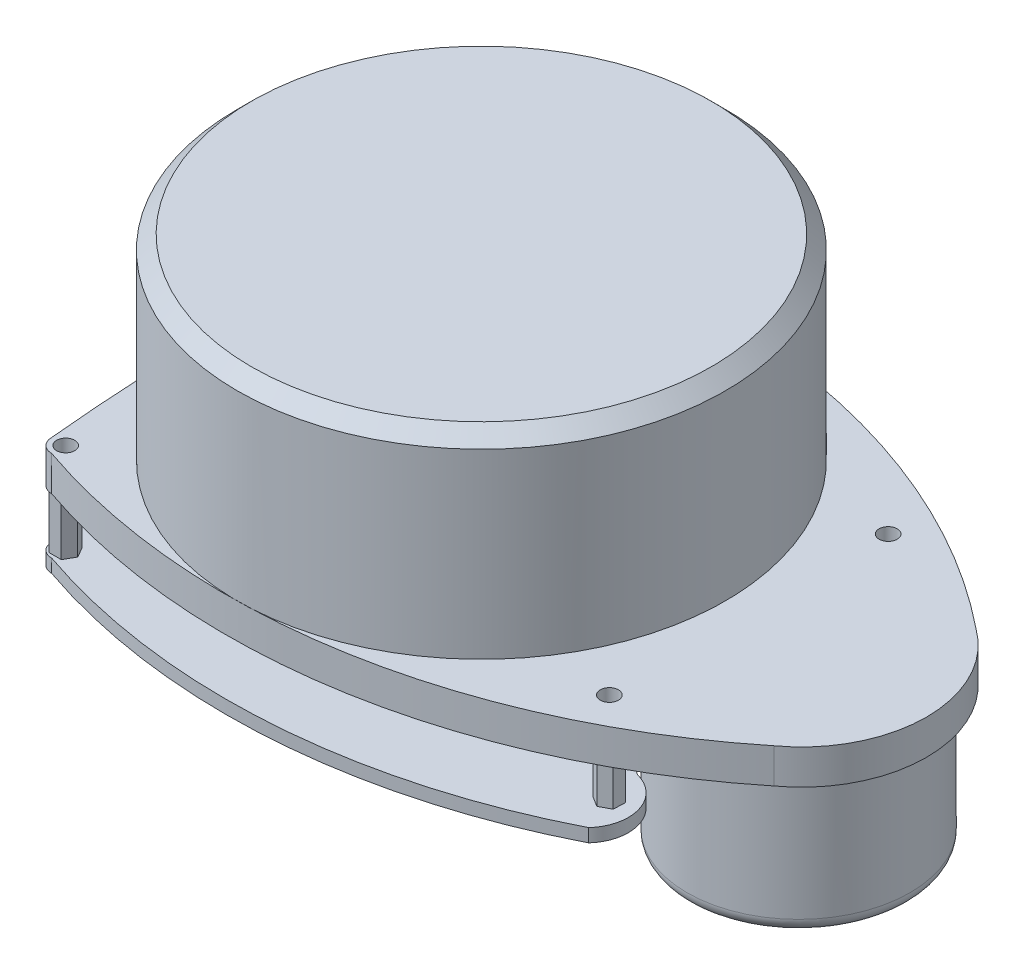
SolidWorks part; units mm, degrees
ref_plane "Front Plane" through (0, 0, 0) normal (0, 0, 1) x (1, 0, 0)
ref_plane "Top Plane" through (0, 0, 0) normal (0, 1, 0) x (1, 0, 0)
ref_plane "Right Plane" through (0, 0, 0) normal (1, 0, 0) x (0, 0, -1)
sketch "Sketch3" plane through (0, 0, 0) normal (0, 1, 0) x (1, 0, 0)
  line L0 (49.25, 0) -> (-49.25, 0) construction
  line L1 (49.25, 30) -> (-49.25, 30) construction
  line L2 (49.25, 30) -> (49.25, -30) construction
  line L3 (49.25, -30) -> (-49.25, -30) construction
  line L4 (-49.25, 30) -> (-49.25, -30) construction
  line L5 (49.25, 30) -> (-49.25, -30) construction
  line L6 (49.25, -30) -> (-49.25, 30) construction
  circle A0 centre (-46.25, 28) radius 1.3
  circle A1 centre (-46.25, -28) radius 1.3
  circle A2 centre (23.75, 20) radius 1.3
  circle A3 centre (23.75, -20) radius 1.3
  arc A5 (-46.25, 30) -> (-48.25, 28) centre (-46.25, 28) ccw
  arc A6 (-48.25, -28) -> (-46.25, -30) centre (-46.25, -28) ccw
  arc A7 (41.8569, 14.5021) -> (-46.25, 30) centre (-16.1861, -57.2803) ccw
  arc A8 (41.8569, -14.5021) -> (-46.25, -30) centre (-16.1861, 57.2803) cw
  arc A9 (-48.25, 28) -> (-48.25, -28) centre (239.7946, 0) ccw
  circle A10 centre (-14.25, 0) radius 35 construction
  arc A11 (41.8569, -14.5021) -> (41.8569, 14.5021) centre (31.3301, 0) ccw
  point P0 (0, 0)
  dimension "D3" = 2.6
  dimension "D12" = 70
  dimension "D1" = 98.5
  dimension "D2" = 60
  dimension "D4" = 56
  dimension "D5" = 28
  dimension "D6" = 70
  dimension "D7" = 70
  dimension "D8" = 40
  dimension "D9" = 20
  dimension "D10" = 3
extrude "Boss-Extrude2" add sketch "Sketch3" along normal blind 5
sketch "Sketch5" plane through (0, 5, 0) normal (0, 1, 0) x (1, 0, 0)
  line L0 (-49.6077, 0) -> (49.25, 0) construction
  arc A0 (-48.25, 28) -> (-48.25, -28) centre (239.7946, 0) ccw construction
  arc A1 (41.8569, -14.5021) -> (41.8569, 14.5021) centre (31.3301, 0) ccw construction
  circle A2 centre (-14.6077, 0) radius 35
  dimension "D1" = 70
extrude "Boss-Extrude4" add sketch "Sketch5" along normal blind 28.1
chamfer "Chamfer2" distance 2 angle 45 1 edges at (-14.6077, 33.1, 35)
sketch "Sketch6" plane through (0, 0, 0) normal (0, -1, 0) x (1, 0, 0)
  line L0 (-49.6077, 0) -> (4.5785, 0) construction
  arc A0 (-48.25, 28) -> (-48.25, -28) centre (239.7946, 0) ccw construction
  circle A1 centre (-14.6077, 0) radius 25
  dimension "D2" = 50
  dimension "D1" = 35
extrude "Boss-Extrude5" add sketch "Sketch6" along normal blind 3
chamfer "Chamfer3" distance 1 angle 45 1 edges at (-14.6077, -3, -25)
sketch "Sketch7" plane through (0, 0, 0) normal (0, -1, 0) x (1, 0, 0)
  line L0 (49.25, 0) -> (-13.8287, 0) construction
  circle A0 centre (30.8923, 0) radius 16
  arc A1 (41.8569, -14.5021) -> (41.8569, 14.5021) centre (31.3301, 0) ccw construction
  dimension "D1" = 32
  dimension "D2" = 80.5
extrude "Boss-Extrude6" add sketch "Sketch7" along normal blind 20
sketch "Sketch8" plane through (0, -20, 0) normal (0, -1, 0) x (1, 0, 0)
  circle A0 centre (30.8923, 0) radius 3.55
  circle A1 centre (30.8923, 0) radius 16 construction
  dimension "D1" = 7.1
extrude "Boss-Extrude7" add sketch "Sketch8" along normal blind 2
fillet "Fillet1" radius 2 1 edges at (30.8923, -20, -16)
sketch "Sketch9" plane through (0, 0, 0) normal (0, -1, 0) x (1, 0, 0)
  line L1 (22.6677, -18.6477) -> (22.0377, -20.2611)
  line L2 (22.0377, -20.2611) -> (23.12, -21.6134)
  line L3 (23.12, -21.6134) -> (24.8323, -21.3523)
  line L4 (24.8323, -21.3523) -> (25.4623, -19.7389)
  line L5 (25.4623, -19.7389) -> (24.38, -18.3866)
  line L6 (24.38, -18.3866) -> (22.6677, -18.6477)
  line L7 (-47.2786, -26.6064) -> (-47.9712, -28.194)
  line L8 (-47.9712, -28.194) -> (-46.9426, -29.5876)
  line L9 (-46.9426, -29.5876) -> (-45.2214, -29.3936)
  line L10 (-45.2214, -29.3936) -> (-44.5288, -27.806)
  line L11 (-44.5288, -27.806) -> (-45.5574, -26.4124)
  line L12 (-45.5574, -26.4124) -> (-47.2786, -26.6064)
  line L13 (-47.1173, 29.4993) -> (-47.9821, 27.9985)
  line L14 (-47.9821, 27.9985) -> (-47.1147, 26.4993)
  line L15 (-47.1147, 26.4993) -> (-45.3827, 26.5007)
  line L16 (-45.3827, 26.5007) -> (-44.5179, 28.0015)
  line L17 (-44.5179, 28.0015) -> (-45.3853, 29.5007)
  line L18 (-45.3853, 29.5007) -> (-47.1173, 29.4993)
  line L19 (22.22, 20.8119) -> (22.2819, 19.081)
  line L20 (22.2819, 19.081) -> (23.8118, 18.2691)
  line L21 (23.8118, 18.2691) -> (25.28, 19.1881)
  line L22 (25.28, 19.1881) -> (25.2181, 20.919)
  line L23 (25.2181, 20.919) -> (23.6882, 21.7309)
  line L24 (23.6882, 21.7309) -> (22.22, 20.8119)
  circle A0 centre (-46.25, -28) radius 1.3 construction
  circle A1 centre (23.75, -20) radius 1.3 construction
  circle A2 centre (23.75, 20) radius 1.3 construction
  circle A3 centre (-46.25, 28) radius 1.3 construction
  circle A4 centre (-46.25, -28) radius 1.3
  circle A5 centre (23.75, -20) radius 1.3
  circle A6 centre (23.75, 20) radius 1.3
  circle A7 centre (-46.25, 28) radius 1.3
  circle A8 centre (23.75, -20) radius 1.5 construction
  circle A9 centre (-46.25, -28) radius 1.5 construction
  circle A10 centre (-46.25, 28) radius 1.5 construction
  circle A11 centre (23.75, 20) radius 1.5 construction
  dimension "D2" = 3
  dimension "D3" = 3
  dimension "D1" = 3
extrude "Boss-Extrude8" add sketch "Sketch9" along normal blind 8
ref_plane "Plane2" through (0, -8, 0) normal (0, -1, 0) x (-1, 0, 0)
sketch "Sketch11" plane through (0, -8, 0) normal (0, -1, 0) x (-1, 0, 0)
  arc A0 (46.25, 30) -> (-41.8569, 14.5021) centre (16.1861, -57.2803) ccw construction
  arc A1 (-41.8569, -14.5021) -> (46.25, -30) centre (16.1861, 57.2803) ccw construction
  arc A2 (48.25, -28) -> (48.25, 28) centre (-239.7946, 0) ccw construction
  arc A3 (46.25, -30) -> (48.25, -28) centre (46.25, -28) ccw construction
  arc A4 (48.25, 28) -> (46.25, 30) centre (46.25, 28) ccw construction
  arc A5 (46.25, 30) -> (-25.7467, 24.9592) centre (16.1861, -57.2803) ccw
  arc A6 (-25.7467, -24.9592) -> (46.25, -30) centre (16.1861, 57.2803) ccw
  arc A7 (48.25, -28) -> (48.25, 28) centre (-239.7946, 0) ccw
  arc A8 (46.25, -30) -> (48.25, -28) centre (46.25, -28) ccw
  arc A9 (48.25, 28) -> (46.25, 30) centre (46.25, 28) ccw
  circle A10 centre (-30.8923, 0) radius 16 construction
  circle A11 centre (-30.8923, 0) radius 16 construction
  arc A12 (-22.6982, -14.8948) -> (-24.4748, 15.7422) centre (-30.8923, 0) ccw
  arc A13 (-25.7467, 24.9592) -> (-24.4748, 15.7422) centre (-22.6982, 20.6836) ccw
  arc A14 (-22.6982, -14.8948) -> (-25.7467, -24.9592) centre (-21.1913, -20.8452) ccw
  circle A15 centre (-23.75, 20) radius 1.3 construction
  circle A16 centre (-30.8923, 0) radius 17 construction
  circle A17 centre (-23.75, -20) radius 1.3 construction
  circle A18 centre (46.25, -28) radius 1.3 construction
  circle A19 centre (46.25, 28) radius 1.3 construction
  circle A20 centre (-23.75, 20) radius 1.3
  circle A21 centre (-23.75, -20) radius 1.3
  circle A22 centre (46.25, -28) radius 1.3
  circle A23 centre (46.25, 28) radius 1.3
  point P23 (-13.8923, 0)
  dimension "D1" = 1
extrude "Boss-Extrude9" add sketch "Sketch11" along normal blind 1.9
sketch "Sketch12" plane through (0, -9.9, 0) normal (0, -1, 0) x (1, 0, 0)
  line L0 (25.28, 19.1881) -> (25.2181, 20.919) construction
  line L1 (23.8118, 18.2691) -> (25.28, 19.1881) construction
  line L2 (25.2181, 20.919) -> (23.6882, 21.7309) construction
  line L3 (23.6882, 21.7309) -> (22.22, 20.8119) construction
  line L4 (22.22, 20.8119) -> (22.2819, 19.081) construction
  line L5 (22.2819, 19.081) -> (23.8118, 18.2691) construction
  line L6 (-47.1173, 29.4993) -> (-47.9821, 27.9985) construction
  line L7 (-45.3853, 29.5007) -> (-47.1173, 29.4993) construction
  line L8 (-47.9821, 27.9985) -> (-47.1147, 26.4993) construction
  line L9 (-44.5179, 28.0015) -> (-45.3853, 29.5007) construction
  line L10 (-45.3827, 26.5007) -> (-44.5179, 28.0015) construction
  line L11 (-47.1147, 26.4993) -> (-45.3827, 26.5007) construction
  line L12 (-47.9712, -28.194) -> (-46.9426, -29.5876) construction
  line L13 (-46.9426, -29.5876) -> (-45.2214, -29.3936) construction
  line L14 (-45.2214, -29.3936) -> (-44.5288, -27.806) construction
  line L15 (-44.5288, -27.806) -> (-45.5574, -26.4124) construction
  line L16 (-45.5574, -26.4124) -> (-47.2786, -26.6064) construction
  line L17 (-47.2786, -26.6064) -> (-47.9712, -28.194) construction
  line L18 (23.12, -21.6134) -> (24.8323, -21.3523) construction
  line L19 (24.8323, -21.3523) -> (25.4623, -19.7389) construction
  line L20 (25.4623, -19.7389) -> (24.38, -18.3866) construction
  line L21 (22.0377, -20.2611) -> (23.12, -21.6134) construction
  line L22 (22.6677, -18.6477) -> (22.0377, -20.2611) construction
  line L23 (25.28, 19.1881) -> (25.2181, 20.919)
  line L24 (23.8118, 18.2691) -> (25.28, 19.1881)
  line L25 (25.2181, 20.919) -> (23.6882, 21.7309)
  line L26 (23.6882, 21.7309) -> (22.22, 20.8119)
  line L27 (22.22, 20.8119) -> (22.2819, 19.081)
  line L28 (22.2819, 19.081) -> (23.8118, 18.2691)
  line L29 (-47.1173, 29.4993) -> (-47.9821, 27.9985)
  line L30 (-45.3853, 29.5007) -> (-47.1173, 29.4993)
  line L31 (-47.9821, 27.9985) -> (-47.1147, 26.4993)
  line L32 (-44.5179, 28.0015) -> (-45.3853, 29.5007)
  line L33 (-45.3827, 26.5007) -> (-44.5179, 28.0015)
  line L34 (-47.1147, 26.4993) -> (-45.3827, 26.5007)
  line L35 (-47.9712, -28.194) -> (-46.9426, -29.5876)
  line L36 (-46.9426, -29.5876) -> (-45.2214, -29.3936)
  line L37 (-45.2214, -29.3936) -> (-44.5288, -27.806)
  line L38 (-44.5288, -27.806) -> (-45.5574, -26.4124)
  line L39 (-45.5574, -26.4124) -> (-47.2786, -26.6064)
  line L40 (-47.2786, -26.6064) -> (-47.9712, -28.194)
  line L41 (23.12, -21.6134) -> (24.8323, -21.3523)
  line L42 (24.8323, -21.3523) -> (25.4623, -19.7389)
  line L43 (25.4623, -19.7389) -> (24.38, -18.3866)
  line L44 (22.0377, -20.2611) -> (23.12, -21.6134)
  line L45 (22.6677, -18.6477) -> (22.0377, -20.2611)
  line L46 (24.38, -18.3866) -> (22.6677, -18.6477) construction
  line L47 (24.38, -18.3866) -> (22.6677, -18.6477)
  arc A8 (-48.25, -28) -> (-46.25, -30) centre (-46.25, -28) ccw
  arc A9 (-46.25, -30) -> (25.7467, -24.9592) centre (-16.1861, 57.2803) ccw
  arc A10 (25.7467, -24.9592) -> (24.4748, -15.7422) centre (22.6982, -20.6836) ccw
  arc A11 (22.6982, 14.8948) -> (24.4748, -15.7422) centre (30.8923, 0) ccw
  arc A12 (22.6982, 14.8948) -> (25.7467, 24.9592) centre (21.1913, 20.8452) ccw
  arc A13 (25.7467, 24.9592) -> (-46.25, 30) centre (-16.1861, -57.2803) ccw
  arc A14 (-46.25, 30) -> (-48.25, 28) centre (-46.25, 28) ccw
  arc A15 (-48.25, 28) -> (-48.25, -28) centre (239.7946, 0) ccw
  arc A16 (-48.25, -28) -> (-46.25, -30) centre (-46.25, -28) ccw
  dimension "D1" = 0
extrude "Boss-Extrude10" [suppressed] add sketch "Sketch12" along normal blind 15 contours L35 L36 L37 L38 L39 L40 | L33 L32 L30 L29 L31 L34 | L28 L24 L23 L25 L26 L27 | L43 L47 L45 L44 L41 L42
